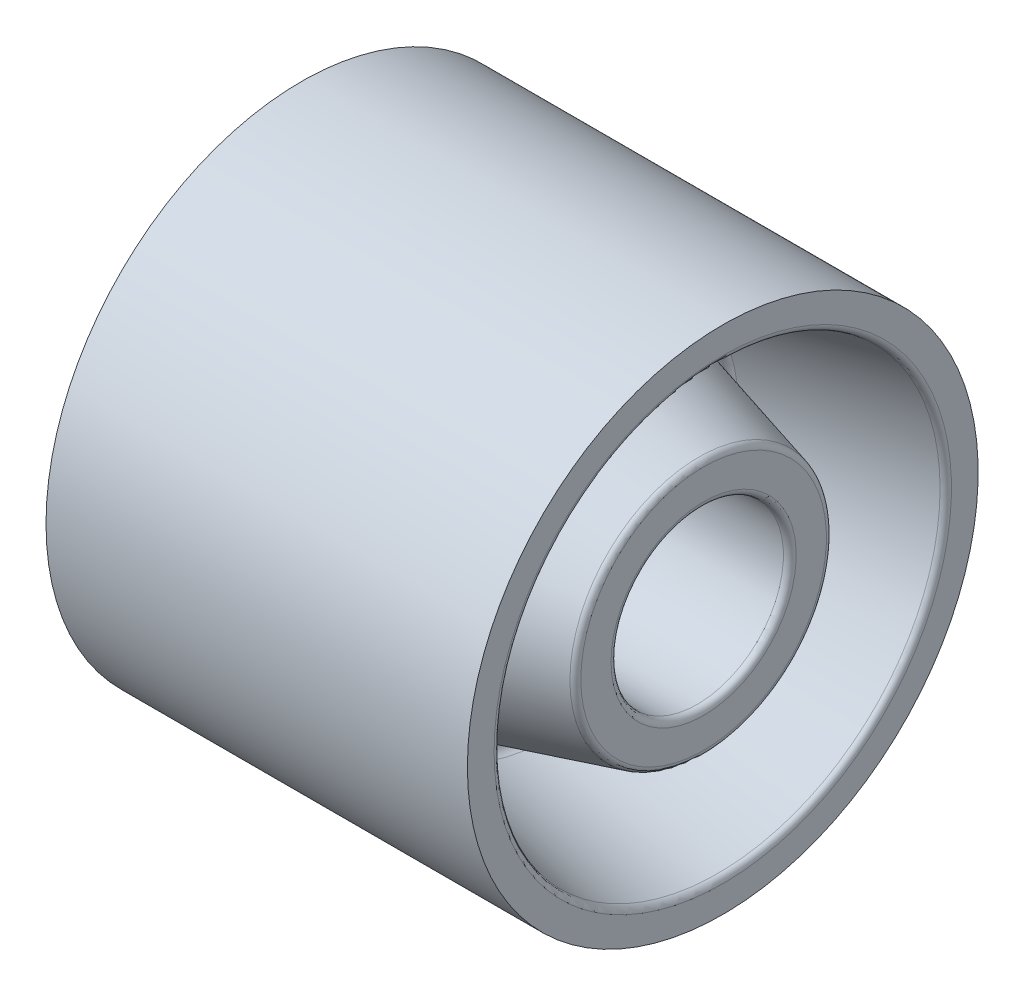
SolidWorks part; units mm, degrees
ref_plane "Front Plane" through (0, 0, 0) normal (0, 0, 1) x (1, 0, 0)
ref_plane "Top Plane" through (0, 0, 0) normal (0, 1, 0) x (1, 0, 0)
ref_plane "Right Plane" through (0, 0, 0) normal (1, 0, 0) x (0, 0, -1)
sketch "Sketch1" plane through (0, 0, 0) normal (0, 0, 1) x (1, 0, 0)
  line L0 (-33, 0) -> (33, 0) construction
  line L1 (-30, 13.5) -> (30, 13.5)
  line L2 (30, 13.5) -> (30, 20)
  line L3 (30, 20) -> (5.6109, 26.5514)
  line L4 (6, 29.5) -> (33, 35)
  line L5 (33, 35) -> (33, 40)
  line L6 (33, 40) -> (-33, 40)
  line L11 (0, 40) -> (0, 0) construction
  line L12 (-30, 13.5) -> (-30, 20)
  line L13 (-30, 20) -> (-5.6109, 26.5514)
  line L14 (-6, 29.5) -> (-33, 35)
  line L15 (-33, 35) -> (-33, 40)
  arc A0 (5.6109, 26.5514) -> (6, 29.5) centre (6, 28) cw
  arc A2 (-5.6109, 26.5514) -> (-6, 29.5) centre (-6, 28) ccw
  point P4 (0, 0)
  point P14 (0, 13.5)
  dimension "D2" = 12
  dimension "D3" = 1.5
  dimension "D4" = 27
  dimension "D9" = 60
  dimension "D1" = 66
  dimension "D5" = 56
  dimension "D6" = 40
  dimension "D7" = 80
  dimension "D8" = 70
revolve "Revolve1" add sketch "Sketch1" angle 360 about L0
fillet "Fillet1" radius 1 6 edges at (30, 0, 13.5) (30, 0, 20) (-30, 0, 20) (-30, 0, 13.5) (33, 0, 35) (-33, 0, 35)
